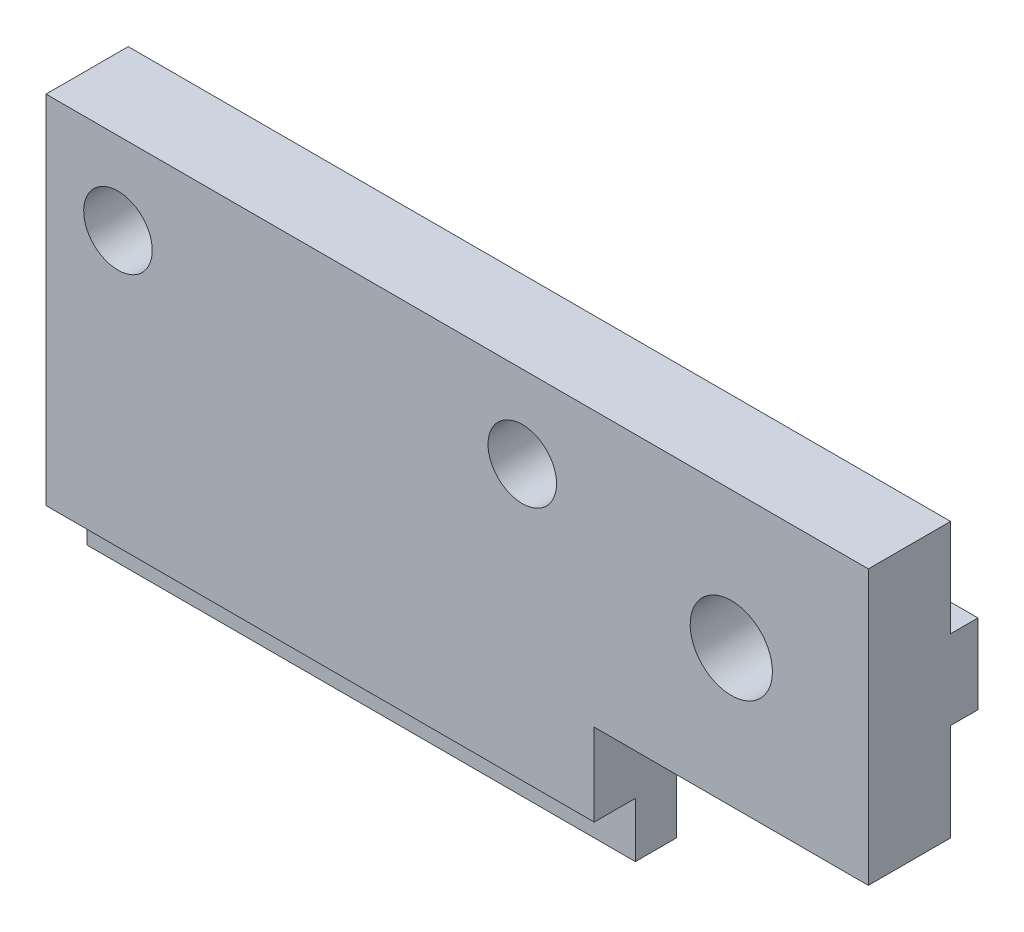
SolidWorks part; units mm, degrees
ref_plane "Front Plane" through (0, 0, 0) normal (0, 0, 1) x (1, 0, 0)
ref_plane "Top Plane" through (0, 0, 0) normal (0, 1, 0) x (1, 0, 0)
ref_plane "Right Plane" through (0, 0, 0) normal (1, 0, 0) x (0, 0, -1)
sketch "Sketch1" plane through (0, 0, 0) normal (0, 0, 1) x (1, 0, 0)
  line L0 (-7.375, 4.5) -> (7.375, 4.5) construction
  line L1 (-10, -7.5) -> (10, -7.5)
  line L2 (-10, -7.5) -> (-10, 7.5)
  line L3 (-10, 7.5) -> (20, 7.5)
  line L4 (10, -7.5) -> (10, -2.5)
  line L5 (-10, -7.5) -> (10, 7.5) construction
  line L6 (-10, 7.5) -> (10, -7.5) construction
  line L7 (10, -2.5) -> (20, -2.5)
  line L8 (20, -2.5) -> (20, 7.5)
  circle A0 centre (-7.375, 4.5) radius 1.25
  circle A1 centre (7.375, 4.5) radius 1.25
  circle A2 centre (15, 2.5) radius 1.5
  point P0 (0, 0)
  point P10 (0, 4.5)
  dimension "D2" = 3
  dimension "D3" = 2.5
  dimension "D9" = 3
  dimension "D1" = 5
  dimension "D4" = 15
  dimension "D5" = 14.75
  dimension "D6" = 20
  dimension "D7" = 10
  dimension "D8" = 10
  dimension "D10" = 5
  dimension "D11" = 5
extrude "Main" add sketch "Sketch1" along normal blind 3
sketch "Sketch2" plane through (0, 0, 3) normal (0, 0, 1) x (1, 0, 0)
  line L0 (-10, 7.5) -> (-10, -7.5) construction
  line L1 (-10, -7.5) -> (10, -7.5)
  line L2 (-10, -7.5) -> (-10, -5.5)
  line L3 (-10, -5.5) -> (10, -5.5)
  line L4 (10, -7.5) -> (10, -5.5)
  line L6 (10, -7.5) -> (10, -2.5) construction
  point P6 (0, 0)
  point P7 (10, -5.5623)
  point P8 (10, -7.5)
  point P10 (0, 0)
  point P13 (10, -7.5)
  dimension "D1" = 2
extrude "PinHoles" cut sketch "Sketch2" against normal blind 1.5
sketch "Sketch3" plane through (-10, 0, 0) normal (-1, 0, 0) x (0, 0, 1)
  line L0 (0, 7.5) -> (0, -7.5) construction
  line L1 (0, 3.95) -> (-1, 3.95)
  line L2 (0, 3.95) -> (0, 1.05)
  line L3 (0, 1.05) -> (-1, 1.05)
  line L4 (-1, 3.95) -> (-1, 1.05)
  line L5 (3, 7.5) -> (0, 7.5) construction
  dimension "D1" = 2.9
  dimension "D2" = 1
  dimension "D3" = 3.55
extrude "MakerBeamSupport" add sketch "Sketch3" against normal up to surface (30 mm away) up to face at (20, 2.5, 1.5)
sketch "Sketch4" plane through (0, 0, 3) normal (0, 0, 1) x (1, 0, 0)
  circle A0 centre (-7.375, 4.5) radius 1.25
  circle A1 centre (7.375, 4.5) radius 1.25
  circle A2 centre (7.375, 4.5) radius 1.25 construction
  circle A3 centre (15, 2.5) radius 1.5
  circle A4 centre (15, 2.5) radius 1.5 construction
  circle A5 centre (-7.375, 4.5) radius 1.25 construction
extrude "Holes2" cut sketch "Sketch4" against normal through all
